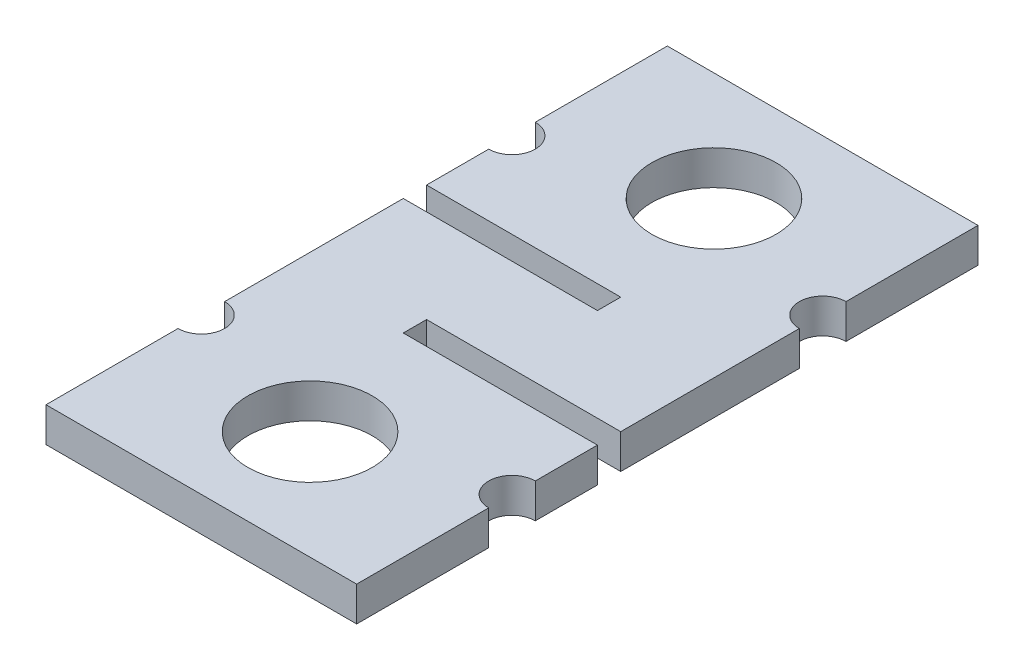
SolidWorks part; units mm, degrees
ref_plane "Alzado" through (0, 0, 0) normal (0, 0, 1) x (1, 0, 0)
ref_plane "Planta" through (0, 0, 0) normal (0, 1, 0) x (1, 0, 0)
ref_plane "Vista lateral" through (0, 0, 0) normal (1, 0, 0) x (0, 0, -1)
sketch "Croquis1" plane through (0, 0, 0) normal (0, 1, 0) x (1, 0, 0)
  line L87 (-20, -41.25) -> (20, -41.25)
  line L88 (-20, -41.25) -> (-20, -24.25)
  line L89 (-5, -10.25) -> (-5, -7.25)
  line L90 (20, -7.25) -> (-5, -7.25)
  line L91 (20, -10.25) -> (-5, -10.25)
  line L92 (5, 7.75) -> (5, 4.75)
  line L93 (-20, 4.75) -> (5, 4.75)
  line L94 (-20, 7.75) -> (5, 7.75)
  line L95 (-20, 7.75) -> (-20, 15.75)
  line L96 (20, -7.25) -> (20, 15.75)
  line L97 (20, -18.25) -> (20, -10.25)
  line L98 (20, -41.25) -> (20, -24.25)
  line L99 (-20, -18.25) -> (-20, 4.75)
  line L100 (-20, 21.75) -> (-20, 38.75)
  line L101 (-20, 38.75) -> (20, 38.75)
  line L102 (20, 21.75) -> (20, 38.75)
  circle A43 centre (0, -27.25) radius 8
  circle A44 centre (0, 24.75) radius 8
  arc A45 (-20, 15.75) -> (-20, 21.75) centre (-20, 18.75) ccw
  arc A46 (20, -18.25) -> (20, -24.25) centre (20, -21.25) ccw
  arc A47 (-20, -24.25) -> (-20, -18.25) centre (-20, -21.25) ccw
  arc A48 (20, 21.75) -> (20, 15.75) centre (20, 18.75) ccw
extrude "Saliente-Extruir1" add sketch "Croquis1" along normal blind 4.45
